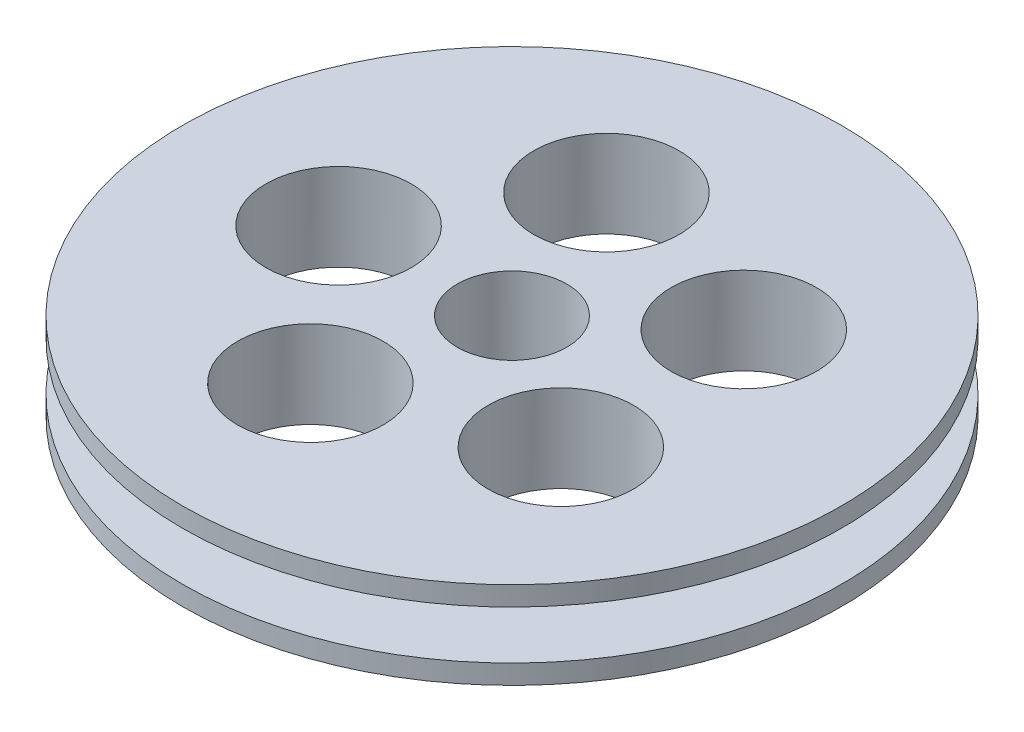
SolidWorks part; units mm, degrees
ref_plane "Front Plane" through (0, 0, 0) normal (0, 0, 1) x (1, 0, 0)
ref_plane "Top Plane" through (0, 0, 0) normal (0, 1, 0) x (1, 0, 0)
ref_plane "Right Plane" through (0, 0, 0) normal (1, 0, 0) x (0, 0, -1)
sketch "Sketch1" plane through (0, 0, 0) normal (1, 0, 0) x (0, 0, -1)
  line L0 (0, 2.5) -> (-4, 2.5) construction
  line L1 (0, 0) -> (30, 0)
  line L2 (0, 0) -> (0, -2)
  line L3 (0, -2) -> (30, -2)
  line L4 (30, 0) -> (30, -2)
  line L5 (0, 0) -> (22, 0)
  line L6 (0, 0) -> (0, 5)
  line L7 (0, 5) -> (22, 5)
  line L8 (22, 0) -> (22, 5)
  line L9 (0, 5) -> (30, 5)
  line L10 (0, 5) -> (0, 7)
  line L11 (0, 7) -> (30, 7)
  line L12 (30, 5) -> (30, 7)
  line L13 (-4, 2.5) -> (-4, 20.0021) construction
  dimension "D1" = 2
  dimension "D2" = 5
  dimension "D3" = 30
  dimension "D4" = 22
  dimension "D5" = 4
revolve "Revolve4" add sketch "Sketch1" angle 360 about L13
sketch "Sketch3" plane through (0, 7, 0) normal (0, 1, 0) x (1, 0, 0)
  circle A0 centre (0, -4) radius 5.6537
  circle A1 centre (0, -4) radius 4 construction
  circle A2 centre (-16.9752, -4.9176) radius 7.5
  circle A3 centre (-6.1183, 11.8608) radius 7.5
  circle A4 centre (13.1939, 6.7201) radius 7.5
  circle A5 centre (14.2726, -13.2354) radius 7.5
  circle A6 centre (-4.373, -20.4279) radius 7.5
  point P17 (0, -4)
  dimension "D2" = 15
  dimension "D1" = 17
  dimension "D3" = 5
extrude "Cut-Extrude1" cut sketch "Sketch3" against normal blind 10
